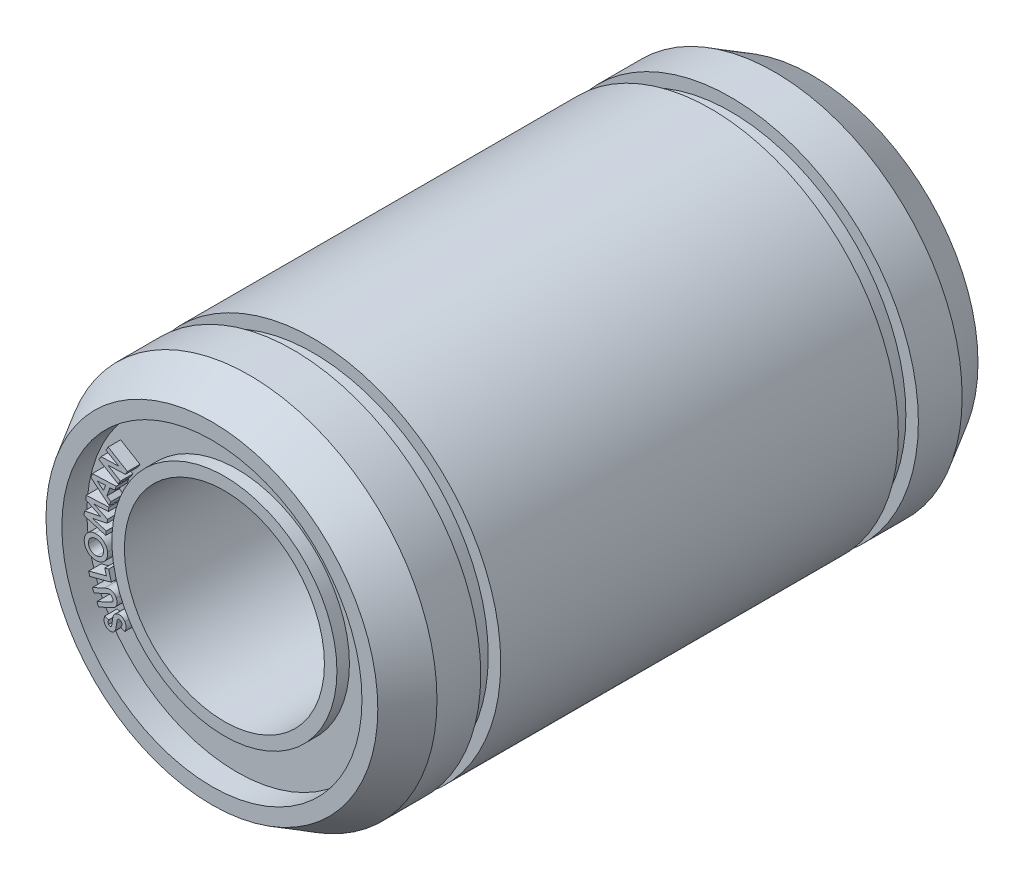
SolidWorks part; units mm, degrees
ref_plane "Front Plane" through (0, 0, 0) normal (0, 0, 1) x (1, 0, 0)
ref_plane "Top Plane" through (0, 0, 0) normal (0, 1, 0) x (1, 0, 0)
ref_plane "Right Plane" through (0, 0, 0) normal (1, 0, 0) x (0, 0, -1)
sketch "Sketch1" plane through (0, 0, 0) normal (0, 0, 1) x (1, 0, 0)
  circle A0 centre (0, 0) radius 7.5
  circle A1 centre (0, 0) radius 6
  dimension "D1" = 15
  dimension "D2" = 12
extrude "Boss-Extrude1" add sketch "Sketch1" along normal mid plane 24
chamfer "Chamfer2" distance 1.5 angle 30 1 edges at (7.5, 0, 12)
sketch "Sketch5" plane through (0, 0, 0) normal (0, 0, 1) x (1, 0, 0)
  circle A0 centre (0, 0) radius 6
  circle A1 centre (0, 0) radius 4
  dimension "D1" = 8
extrude "Boss-Extrude2" add sketch "Sketch5" along normal blind 11 and the other way blind 11 separate body
sketch "Sketch6" plane through (0, 0, 11) normal (0, 0, 1) x (1, 0, 0)
  circle A0 centre (0, 0) radius 4
  circle A1 centre (0, 0) radius 4.5
  dimension "D1" = 9
extrude "Boss-Extrude3" add sketch "Sketch6" along normal blind 0.5
mirror "Mirror1" about plane through (0, 0, 0) normal (0, 0, 1) of "Boss-Extrude3"
sketch "Sketch7" plane through (0, 0, 0) normal (1, 0, 0) x (0, 0, -1)
  line L0 (12, 7.5) -> (-10.5, 7.5) construction
  line L1 (-8.75, 7.5) -> (-7.95, 7.5)
  line L2 (-8.75, 7.5) -> (-8.75, 7)
  line L3 (-8.75, 7) -> (-7.95, 7)
  line L4 (-7.95, 7.5) -> (-7.95, 7)
  line L5 (0, 0) -> (5.2365, 0) construction
  line L6 (7.95, 7.5) -> (8.75, 7.5)
  line L7 (7.95, 7.5) -> (7.95, 7)
  line L8 (7.95, 7) -> (8.75, 7)
  line L9 (8.75, 7.5) -> (8.75, 7)
  dimension "D1" = 17.5
  dimension "D2" = 0.8
  dimension "D3" = 0.8
  dimension "D4" = 7.95
  dimension "D5" = 0.5
  dimension "D6" = 0.5
revolve "Cut-Revolve1" cut sketch "Sketch7" angle 360 about L5
sketch "Sketch8" plane through (0, 0, 11) normal (0, 0, 1) x (1, 0, 0)
  circle A0 centre (0, 0) radius 4.7503 construction
  text T0 "SULOMAN" font "Century Gothic" height 0.9
extrude "Boss-Extrude4" add sketch "Sketch8" along normal blind 0.5
ref_plane "Plane1" through (7.5, 0, 0) normal (1, 0, 0) x (0, 0, -1)
chamfer "Chamfer3" distance 1.5 angle 30 1 edges at (7.5, 0, -12)
